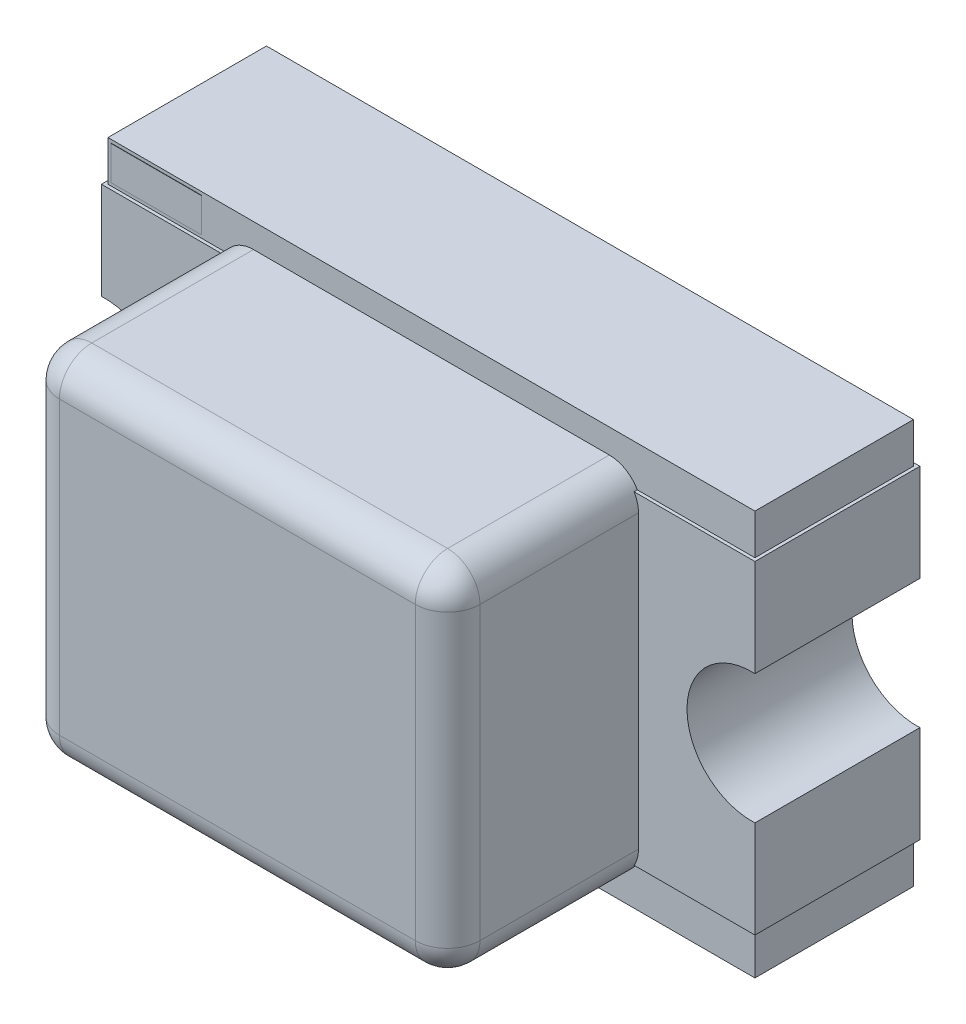
SolidWorks part; units mm, degrees
ref_plane "Спереди" through (0, 0, 0) normal (0, 0, 1) x (1, 0, 0)
ref_plane "Сверху" through (0, 0, 0) normal (0, 1, 0) x (1, 0, 0)
ref_plane "Справа" through (0, 0, 0) normal (1, 0, 0) x (0, 0, -1)
sketch "Эскиз2" plane through (0, 0, 0) normal (0, 0, 1) x (1, 0, 0)
  line L1 (-1, 0.625) -> (1, 0.625)
  line L2 (-1, 0.625) -> (-1, -0.625)
  line L3 (-1, -0.625) -> (1, -0.625)
  line L4 (1, 0.625) -> (1, -0.625)
  point P0 (0, 0)
extrude "Бобышка-Вытянуть1" add sketch "Эскиз2" along normal blind 0.49 from offset 0.01
sketch "Эскиз3" plane through (0, 0, 0) normal (0, 0, 1) x (1, 0, 0)
  line L1 (-1.01, 0.5) -> (-0.6, 0.5)
  line L2 (-1.01, 0.5) -> (-1.01, -0.5)
  line L3 (-1.01, -0.5) -> (-0.6, -0.5)
  line L4 (-0.6, 0.5) -> (-0.6, -0.5)
  line L5 (0.6, 0.5) -> (1.01, 0.5)
  line L6 (0.6, 0.5) -> (0.6, -0.5)
  line L7 (0.6, -0.5) -> (1.01, -0.5)
  line L8 (1.01, 0.5) -> (1.01, -0.5)
extrude "Бобышка-Вытянуть2" add sketch "Эскиз3" along normal blind 0.51
sketch "Эскиз4" plane through (0, 0, 0) normal (0, 0, 1) x (1, 0, 0)
  line L1 (-0.65, 0.55) -> (0.65, 0.55)
  line L2 (-0.65, 0.55) -> (-0.65, -0.55)
  line L3 (-0.65, -0.55) -> (0.65, -0.55)
  line L4 (0.65, 0.55) -> (0.65, -0.55)
extrude "Бобышка-Вытянуть3" add sketch "Эскиз4" along normal blind 0.6 from offset 0.5
fillet "Скругление1" radius 0.1 8 edges at (0.65, 0.55, 0.8) (-0.65, 0.55, 0.8) (0, 0.55, 1.1) (0.65, 0, 1.1) (0.65, -0.55, 0.8) (-0.65, -0.55, 0.8) (0, -0.55, 1.1) (-0.65, 0, 1.1)
sketch "Эскиз5" plane through (0, 0, 0.5) normal (0, 0, 1) x (1, 0, 0)
  line L1 (-0.99, 0.615) -> (-0.71, 0.615)
  line L2 (-0.99, 0.615) -> (-0.99, 0.51)
  line L3 (-0.99, 0.51) -> (-0.71, 0.51)
  line L4 (-0.71, 0.615) -> (-0.71, 0.51)
  line L5 (-0.99, -0.51) -> (-0.71, -0.51)
  line L6 (-0.99, -0.51) -> (-0.99, -0.615)
  line L7 (-0.99, -0.615) -> (-0.71, -0.615)
  line L8 (-0.71, -0.51) -> (-0.71, -0.615)
extrude "Бобышка-Вытянуть4" add sketch "Эскиз5" along normal blind 0.001
sketch "Эскиз6" plane through (0, 0, 0) normal (0, 0, 1) x (1, 0, 0)
  circle A0 centre (-1, 0) radius 0.2
  circle A1 centre (1, 0) radius 0.2
extrude "Вырез-Вытянуть2" cut sketch "Эскиз6" along normal blind 0.52
